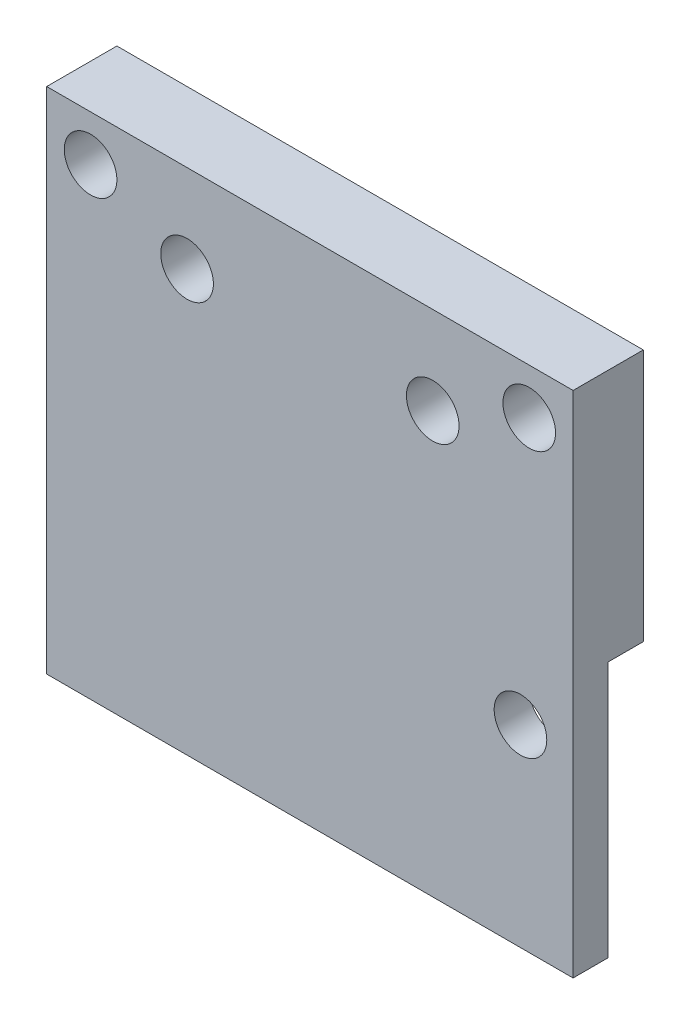
SolidWorks part; units mm, degrees
ref_plane "Plano frontal" through (0, 0, 0) normal (0, 0, 1) x (1, 0, 0)
ref_plane "Plano superior" through (0, 0, 0) normal (0, 1, 0) x (1, 0, 0)
ref_plane "Plano direito" through (0, 0, 0) normal (1, 0, 0) x (0, 0, -1)
sketch "Esboço3" plane through (0, 0, 0) normal (0, 0, 1) x (1, 0, 0)
  line L0 (-15, -22.5) -> (15, 7.5) construction
  line L1 (-15, -22.5) -> (15, -22.5)
  line L2 (-15, -22.5) -> (-15, 22.5)
  line L3 (-15, 22.5) -> (15, 22.5)
  line L4 (15, -22.5) -> (15, 22.5)
  line L5 (-15, -22.5) -> (15, 22.5) construction
  line L6 (-15, 22.5) -> (15, -22.5) construction
  line L7 (0, -7.5) -> (15, -22.5) construction
  line L8 (0, 14.6722) -> (0, 0) construction
  line L9 (15, -6.5) -> (-15, -6.5)
  circle A0 centre (12, 4.5) radius 1.5
  circle A1 centre (-12, -19.5) radius 1.5
  circle A2 centre (-12.5, 19.8979) radius 1.5
  circle A3 centre (12.5, 19.8979) radius 1.5
  circle A4 centre (-7, 17.5) radius 1.5
  circle A5 centre (7, 17.5) radius 1.5
  point P0 (0, 0)
  dimension "D2" = 3
  dimension "D5" = 3
  dimension "D1" = 3
  dimension "D3" = 30
  dimension "D4" = 29
  dimension "D6" = 14
  dimension "D7" = 25
  dimension "D8" = 6
  dimension "D9" = 5
  dimension "D10" = 11
extrude "Ressalto-extrusão2" add sketch "Esboço3" along normal blind 4 contours L9 L4 L3 L2 A5 A4 A3 A2 A0
sketch "Esboço5" plane through (0, 0, 0) normal (0, 0, -1) x (-1, 0, 0)
  line L0 (-15, -6.5) -> (-15, 22.5) construction
  line L1 (-15, 8.1) -> (15, 8.1)
  line L2 (-15, 8.1) -> (-15, -6.5)
  line L3 (-15, -6.5) -> (15, -6.5)
  line L4 (15, 8.1) -> (15, -6.5)
  circle A0 centre (-12, 4.5) radius 1.5 construction
  dimension "D1" = 3.6
extrude "Corte-extrusão2" cut sketch "Esboço5" against normal blind 2
